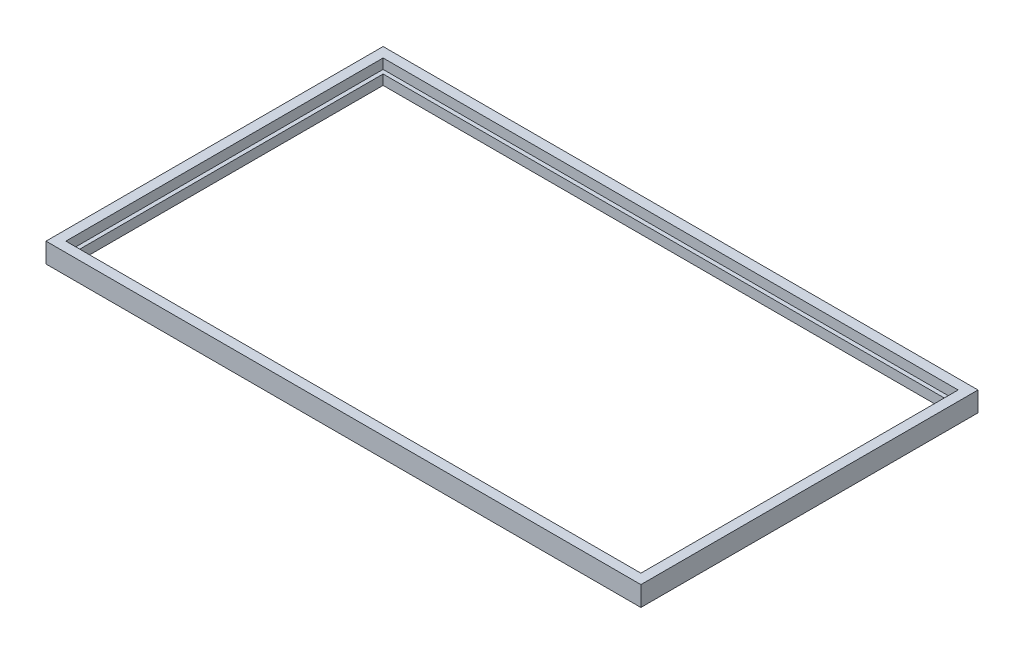
SolidWorks part; units mm, degrees
ref_plane "Front Plane" through (0, 0, 0) normal (0, 0, 1) x (1, 0, 0)
ref_plane "Top Plane" through (0, 0, 0) normal (0, 1, 0) x (1, 0, 0)
ref_plane "Right Plane" through (0, 0, 0) normal (1, 0, 0) x (0, 0, -1)
sketch "Sketch1" plane through (0, 0, 0) normal (0, 1, 0) x (1, 0, 0)
  line L1 (-160.5753, 72.0127) -> (139.4247, 72.0127)
  line L2 (-160.5753, 72.0127) -> (-160.5753, -97.9873)
  line L3 (-160.5753, -97.9873) -> (139.4247, -97.9873)
  line L4 (139.4247, 72.0127) -> (139.4247, -97.9873)
  dimension "D1" = 170
  dimension "D2" = 300
extrude "Boss-Extrude1" add sketch "Sketch1" along normal blind 10
sketch "Sketch2" plane through (0, 10, 0) normal (0, 1, 0) x (1, 0, 0)
  line L0 (139.4247, 72.0127) -> (-160.5753, 72.0127) construction
  line L1 (-155.5753, 67.0127) -> (134.4247, 67.0127)
  line L2 (-155.5753, 67.0127) -> (-155.5753, -92.9873)
  line L3 (-155.5753, -92.9873) -> (134.4247, -92.9873)
  line L4 (134.4247, 67.0127) -> (134.4247, -92.9873)
  line L5 (-153.5753, 65.0127) -> (132.4247, 65.0127)
  line L6 (-153.5753, 65.0127) -> (-153.5753, -90.9873)
  line L7 (-153.5753, -90.9873) -> (132.4247, -90.9873)
  line L8 (132.4247, 65.0127) -> (132.4247, -90.9873)
  line L9 (-160.5753, -97.9873) -> (139.4247, -97.9873) construction
  line L10 (-160.5753, 72.0127) -> (-160.5753, -97.9873) construction
  line L11 (139.4247, -97.9873) -> (139.4247, 72.0127) construction
  dimension "D1" = 5
  dimension "D2" = 5
  dimension "D3" = 5
  dimension "D4" = 5
  dimension "D5" = 2
  dimension "D6" = 2
  dimension "D7" = 2
  dimension "D8" = 2
extrude "Cut-Extrude1" cut sketch "Sketch2" against normal blind 5
sketch "Sketch3" plane through (0, 0, 0) normal (0, 1, 0) x (1, 0, 0)
  line L0 (-10.5753, -932.9873) -> (-10.5753, 49067.0127) construction
  line L1 (134.4247, 67.0127) -> (-155.5753, 67.0127) construction
  line L3 (-151.2048, 62.5) -> (45.2452, 62.5)
  line L4 (-151.2048, 62.5) -> (-151.2048, -89.2)
  line L5 (-151.2048, -89.2) -> (45.2452, -89.2)
  line L6 (45.2452, 62.5) -> (45.2452, -89.2)
  point P5 (-10.5753, 67.0127)
  dimension "D1" = 196.45
  dimension "D2" = 151.7
sketch "Sketch5" plane through (0, 10, 0) normal (0, 1, 0) x (1, 0, 0)
  line L1 (-153.5753, 65.0127) -> (132.4247, 65.0127)
  line L2 (-153.5753, 65.0127) -> (-153.5753, -90.9873)
  line L3 (-153.5753, -90.9873) -> (132.4247, -90.9873)
  line L4 (132.4247, 65.0127) -> (132.4247, -90.9873)
extrude "Cut-Extrude2" cut sketch "Sketch5" against normal blind 40 and the other way blind 28
